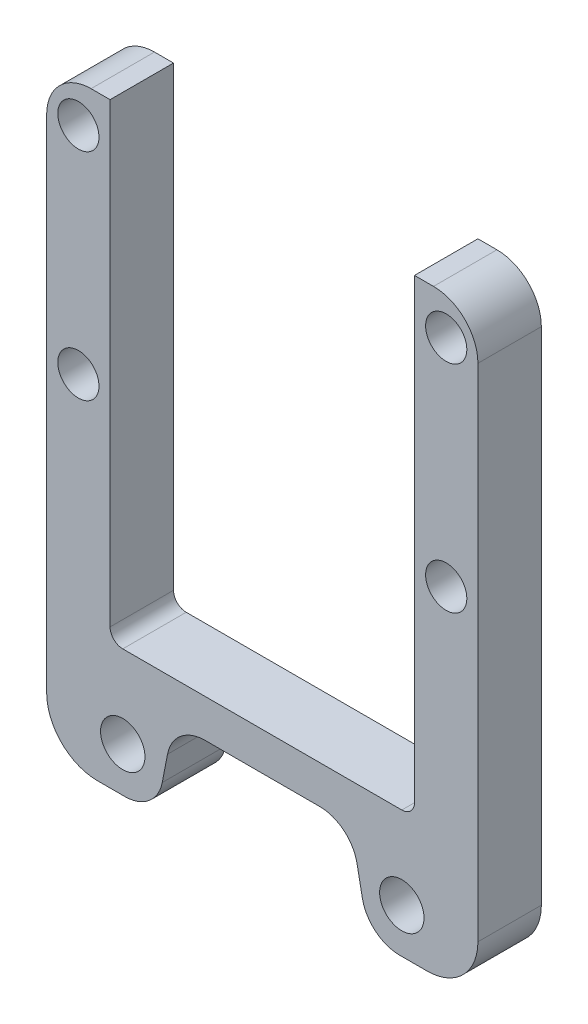
SolidWorks part; units mm, degrees
ref_plane "Plan de face" through (0, 0, 0) normal (0, 0, 1) x (1, 0, 0)
ref_plane "Plan de dessus" through (0, 0, 0) normal (0, 1, 0) x (1, 0, 0)
ref_plane "Plan de droite" through (0, 0, 0) normal (1, 0, 0) x (0, 0, -1)
sketch "Esquisse1" plane through (0, 0, 0) normal (0, 0, 1) x (1, 0, 0)
  line L0 (24, 110) -> (24, 36)
  line L1 (24, 36) -> (0, 36)
  line L7 (0, 30) -> (14, 30)
  line L8 (14, 30) -> (16.7213, 16)
  line L9 (16.7213, 16) -> (34, 16)
  line L10 (34, 16) -> (34, 110)
  line L11 (34, 110) -> (24, 110)
  line L12 (0, 36) -> (0, 30)
  line L13 (0, -0.15) -> (0, 72.4519) construction
  circle A0 centre (29, 104) radius 3.25
  circle A1 centre (22, 23) radius 3.5
  circle A3 centre (29, 70) radius 3.25
  point P5 (0, 0)
  point P17 (22, 17.1434)
  point P19 (29, 110)
  dimension "D9" = 7
  dimension "D10" = 6
  dimension "D14" = 6.5
  dimension "D1" = 6
  dimension "D2" = 24
  dimension "D3" = 101
  dimension "D4" = 30
  dimension "D5" = 10
  dimension "D6" = 74
  dimension "D7" = 14
  dimension "D8" = 14
  dimension "D11" = 34
  dimension "D12" = 7
  dimension "D13" = 22
extrude "Boss.-Extru.1" add sketch "Esquisse1" along normal blind 10
mirror "Symétrie2" about plane through (0, 36, 10) normal (1, 0, 0) of "Boss.-Extru.1"
fillet "Congé1" radius 6 4 edges at (16.7213, 16, 5) (-16.7213, 16, 5) (-14, 30, 5) (14, 30, 5)
fillet "Congé2" radius 8 2 edges at (-34, 16, 5) (34, 16, 5)
fillet "Congé3" radius 7 2 edges at (34, 110, 5) (-34, 110, 5)
fillet "Congé4" radius 2 2 edges at (-24, 36, 5) (24, 36, 5)
